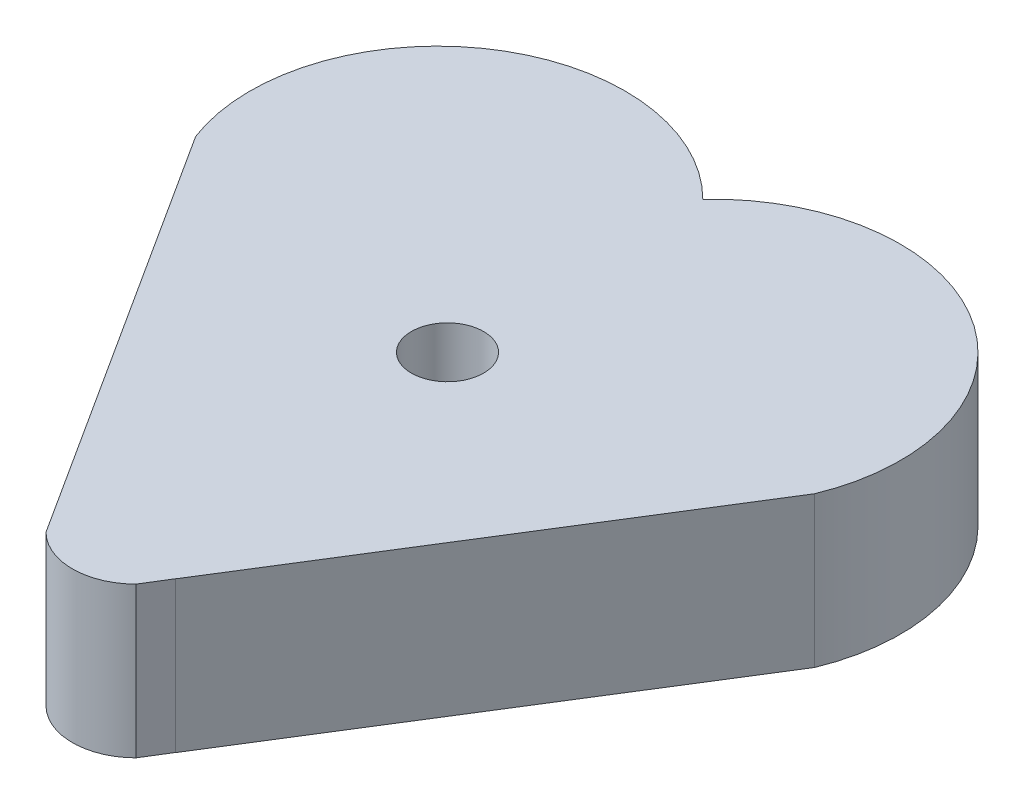
SolidWorks part; units mm, degrees
ref_plane "Front Plane" through (0, 0, 0) normal (0, 0, 1) x (1, 0, 0)
ref_plane "Top Plane" through (0, 0, 0) normal (0, 1, 0) x (1, 0, 0)
ref_plane "Right Plane" through (0, 0, 0) normal (1, 0, 0) x (0, 0, -1)
sketch "Sketch1" plane through (0, 0, 0) normal (0, 1, 0) x (1, 0, 0)
  line L7 (1.519, -12.0337) -> (2.0381, -11.1934)
  line L10 (-10.5612, 2.0606) -> (-1.519, -12.0337)
  line L11 (1.519, -12.0337) -> (10.3292, 2.0606)
  line L12 (-9.2392, 0) -> (-9.2828, 0)
  arc A3 (-2.0139, -11.2622) -> (2.0381, -11.1934) centre (0, -10.5147) ccw
  arc A4 (10.3292, 2.0606) -> (-0.1644, 8.7833) centre (4.477, 4.477) ccw
  arc A5 (-9.2828, 0) -> (-9.1503, -0.1385) centre (-4.6414, 4.3063) ccw
  arc A6 (-0.1644, 8.7833) -> (-10.5612, 2.0606) centre (-4.6414, 4.3063) ccw
  circle A7 centre (0, 0) radius 1.219
extrude "Boss-Extrude6" add sketch "Sketch1" along normal blind 5.08 contours A4 A6 L10 A3 L7 L11 A7
